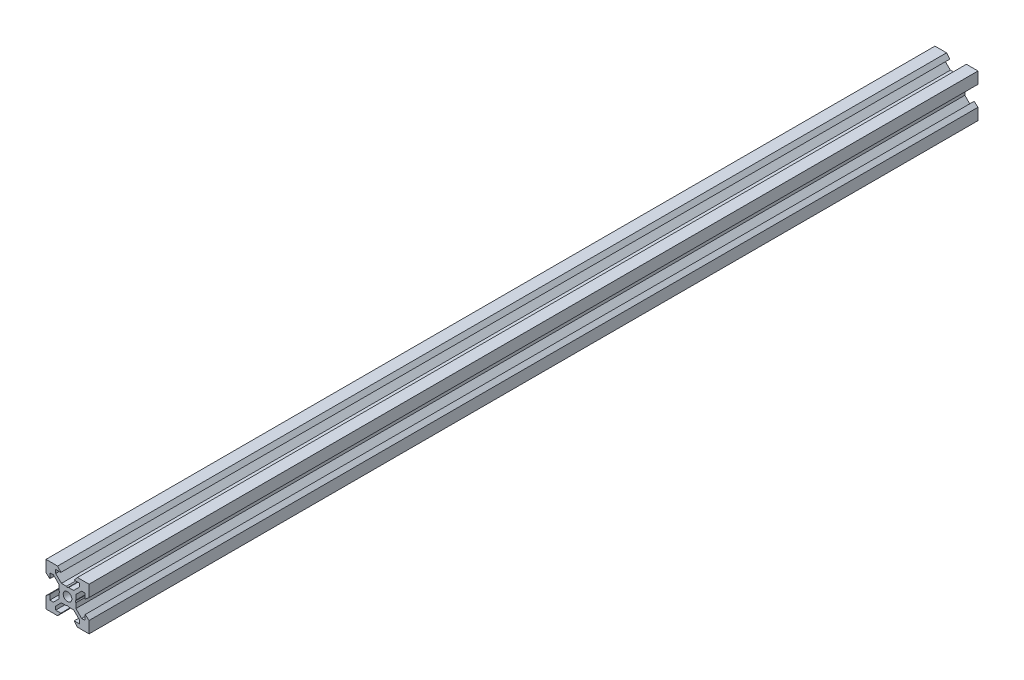
SolidWorks part; units mm, degrees
ref_plane "Front Plane" through (0, 0, 0) normal (0, 0, 1) x (1, 0, 0)
ref_plane "Top Plane" through (0, 0, 0) normal (0, 1, 0) x (1, 0, 0)
ref_plane "Right Plane" through (0, 0, 0) normal (1, 0, 0) x (0, 0, -1)
sketch "Sketch1" plane through (0, 0, 0) normal (0, 0, 1) x (1, 0, 0)
  line L0 (10, 10) -> (4.6104, 10) construction
  line L1 (10, 10) -> (10, 4.6104) construction
  line L2 (10, -10) -> (10, -4.6104) construction
  line L3 (10, -10) -> (4.6104, -10) construction
  line L4 (10, 10) -> (10, 4.6104)
  line L5 (6.5607, 5.5) -> (8.2, 5.5)
  line L6 (5.5, 8.2) -> (5.5, 6.5607)
  line L7 (10, 10) -> (4.6104, 10)
  line L8 (10, 10) -> (10, 4.6104)
  line L9 (6.5607, 5.5) -> (3.9, 2.8393)
  line L10 (5.5, 6.5607) -> (2.8393, 3.9)
  line L11 (10, 4.6104) -> (8.2, 3.1)
  line L12 (4.6104, 10) -> (3.1, 8.2)
  line L13 (8.2, 3.1) -> (8.2, 5.5)
  line L14 (3.1, 8.2) -> (5.5, 8.2)
  line L15 (-6.5607, 5.5) -> (-8.2, 5.5)
  line L16 (6.5607, -5.5) -> (8.2, -5.5)
  line L17 (3.1, -8.2) -> (5.5, -8.2)
  line L18 (8.2, -3.1) -> (8.2, -5.5)
  line L19 (4.6104, -10) -> (3.1, -8.2)
  line L20 (10, -4.6104) -> (8.2, -3.1)
  line L21 (0.5196, -3.9) -> (0, -3.6)
  line L22 (0.5196, 3.9) -> (0, 3.6)
  line L23 (3.6, 0) -> (3.9, -0.5196)
  line L24 (3.9, 0.5196) -> (3.6, 0)
  line L25 (3.9, 0.5196) -> (3.9, 2.8393)
  line L26 (2.8393, 3.9) -> (0.5196, 3.9)
  line L27 (3.9, -2.8393) -> (3.9, -0.5196)
  line L28 (2.8393, -3.9) -> (0.5196, -3.9)
  line L29 (5.5, -6.5607) -> (2.8393, -3.9)
  line L30 (6.5607, -5.5) -> (3.9, -2.8393)
  line L31 (10, -10) -> (10, -4.6104)
  line L32 (10, -10) -> (4.6104, -10)
  line L33 (5.5, -8.2) -> (5.5, -6.5607)
  line L34 (-6.5607, -5.5) -> (-8.2, -5.5)
  line L35 (10, -10) -> (10, -4.6104)
  line L36 (0, 0) -> (0, 8.2) construction
  line L37 (-10, -10) -> (-4.6104, -10) construction
  line L38 (-10, -10) -> (-10, -4.6104) construction
  line L39 (-10, 10) -> (-10, 4.6104) construction
  line L40 (-10, 10) -> (-4.6104, 10) construction
  line L41 (-10, -10) -> (-10, -4.6104)
  line L43 (-5.5, -8.2) -> (-5.5, -6.5607)
  line L44 (-10, -10) -> (-4.6104, -10)
  line L45 (-10, -10) -> (-10, -4.6104)
  line L46 (-6.5607, -5.5) -> (-3.9, -2.8393)
  line L47 (-5.5, -6.5607) -> (-2.8393, -3.9)
  line L48 (-2.8393, -3.9) -> (-0.5196, -3.9)
  line L49 (-3.9, -2.8393) -> (-3.9, -0.5196)
  line L50 (-2.8393, 3.9) -> (-0.5196, 3.9)
  line L51 (-3.9, 0.5196) -> (-3.9, 2.8393)
  line L52 (-3.9, 0.5196) -> (-3.6, 0)
  line L53 (-3.6, 0) -> (-3.9, -0.5196)
  line L54 (-0.5196, 3.9) -> (0, 3.6)
  line L55 (-0.5196, -3.9) -> (0, -3.6)
  line L56 (-10, -4.6104) -> (-8.2, -3.1)
  line L57 (-4.6104, -10) -> (-3.1, -8.2)
  line L58 (-8.2, -3.1) -> (-8.2, -5.5)
  line L59 (-3.1, -8.2) -> (-5.5, -8.2)
  line L60 (-10, -10) -> (10, -10) construction
  line L61 (-10, -10) -> (-10, 10) construction
  line L62 (-3.1, 8.2) -> (-5.5, 8.2)
  line L63 (-8.2, 3.1) -> (-8.2, 5.5)
  line L64 (-4.6104, 10) -> (-3.1, 8.2)
  line L65 (-10, 4.6104) -> (-8.2, 3.1)
  line L66 (-5.5, 6.5607) -> (-2.8393, 3.9)
  line L67 (-6.5607, 5.5) -> (-3.9, 2.8393)
  line L68 (-10, 10) -> (-10, 4.6104)
  line L69 (-10, 10) -> (-4.6104, 10)
  line L70 (-5.5, 8.2) -> (-5.5, 6.5607)
  line L71 (-10, 10) -> (10, 10) construction
  line L72 (-10, 10) -> (-10, 4.6104)
  line L73 (10, -10) -> (10, 10) construction
  line L74 (-10, -10) -> (10, 10) construction
  line L75 (-10, 10) -> (10, -10) construction
  circle A0 centre (0, 0) radius 2
  dimension "D7" = 4
  dimension "D1" = 20
  dimension "D2" = 5.3896
  dimension "D3" = 4.5
  dimension "D4" = 50
  dimension "D5" = 1.8
  dimension "D6" = 1.5104
  dimension "D8" = 5.5
  dimension "D9" = 120
  dimension "D10" = 0.3
  dimension "D11" = 2.3197
  dimension "D12" = 7.8
  dimension "D13" = 7.8
  dimension "D14" = 1.5
  dimension "D15" = 2.6607
extrude "Boss-Extrude1" add sketch "Sketch1" along normal mid plane 413.01 contours L70 L62 L64 L69 L68 L65 L63 L15 L67 L51 L52 L53 L49 L46 L34 L58 L56 L41 L44 L57 L59 L43 L47 L48 L55 L21 L28 L29 L33 L17 L19 L32 L31 L20 L18 L16 L30 L27 L23 L24 L25 L9 L5 L13 L11 L4 L7 L12 L14 L6 L10
